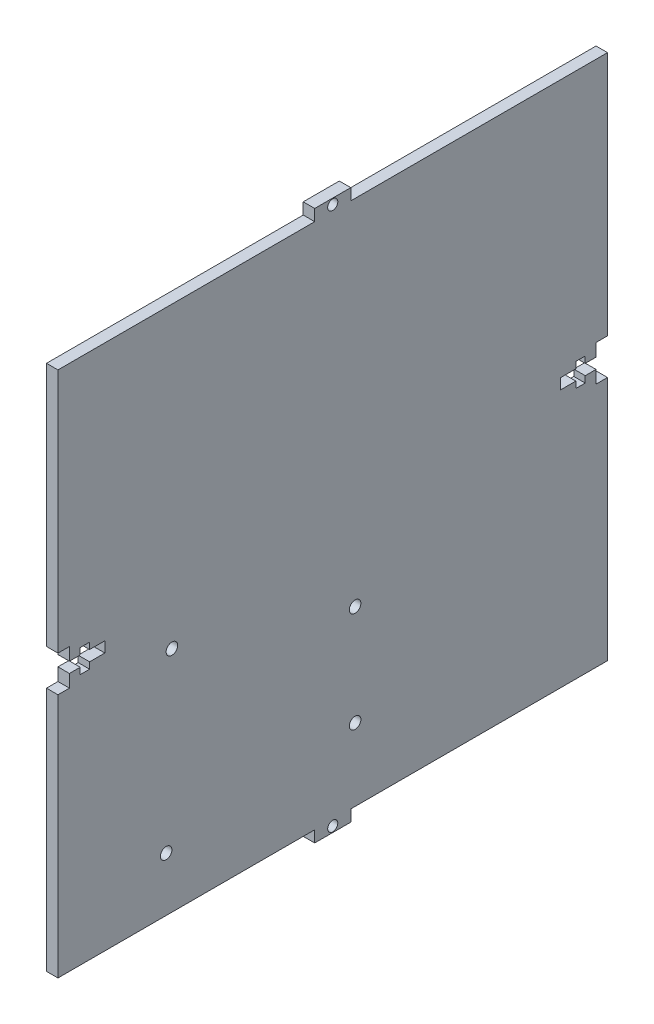
SolidWorks part; units mm, degrees
ref_plane "Front Plane" through (0, 0, 0) normal (0, 0, 1) x (1, 0, 0)
ref_plane "Top Plane" through (0, 0, 0) normal (0, 1, 0) x (1, 0, 0)
ref_plane "Right Plane" through (0, 0, 0) normal (1, 0, 0) x (0, 0, -1)
sketch "Sketch1" plane through (0, 0, 0) normal (1, 0, 0) x (0, 0, -1)
  line L1 (76.2, 73.02) -> (-76.2, 73.02)
  line L2 (76.2, 73.02) -> (76.2, -73.02)
  line L3 (76.2, -73.02) -> (-76.2, -73.02)
  line L4 (-76.2, 73.02) -> (-76.2, -73.02)
  line L5 (76.2, 73.02) -> (-76.2, -73.02) construction
  line L6 (76.2, -73.02) -> (-76.2, 73.02) construction
  point P0 (0, 0)
  dimension "D1" = 146.04
  dimension "D2" = 152.4
extrude "Boss-Extrude1" add sketch "Sketch1" along normal blind 3.18
sketch "Sketch3" plane through (0, 0, 0) normal (-1, 0, 0) x (0, 0, 1)
  line L1 (0, 0) -> (-76.2, 0) construction
  line L2 (-76.2, -73.02) -> (-76.2, 73.02) construction
  line L3 (0, -73.02) -> (0, 73.02) construction
  line L9 (0, 0) -> (76.2, 0) construction
  line L10 (76.2, -73.02) -> (-76.2, -73.02) construction
  line L12 (76.2, 73.02) -> (76.2, -73.02) construction
  line L13 (-76.2, 73.02) -> (76.2, 73.02) construction
  line L14 (5, -73.02) -> (-5, -73.02)
  line L15 (5, -76.2) -> (-5, -76.2)
  line L16 (5, -76.2) -> (5, -73.02)
  line L18 (-5, -76.2) -> (-5, -73.02)
  line L22 (0, -76.2) -> (0, -70.042) construction
  line L23 (5, -74.61) -> (-5, -74.61) construction
  line L27 (5, 73.02) -> (5, 76.2)
  line L28 (5, 76.2) -> (-5, 76.2)
  line L29 (-5, 73.02) -> (-5, 76.2)
  line L30 (5, 74.61) -> (-5, 74.61) construction
  line L31 (0, 73.02) -> (0, 76.2) construction
  line L32 (5, 73.02) -> (-5, 73.02)
  line L33 (0, 57.9987) -> (0, 73.02)
  circle A0 centre (0, -74.61) radius 1.4
  circle A1 centre (0, 74.61) radius 1.4
  point P31 (0, 65.5094)
  line M14 (76.2, 73.02) -> (-76.2, 73.02)
  line M16 (-76.2, -73.02) -> (76.2, -73.02)
  dimension "D5" = 2.8
  dimension "D6" = 2.8
  dimension "D2" = 10
  dimension "D3" = 3.18
  dimension "D4" = 10
  dimension "D1" = 3.18
extrude "Boss-Extrude5" add sketch "Sketch3" against normal blind 3.18 contours L29 L32 L27 L28 A1 M14 | L18 L15 L16 A0 M16
sketch "Sketch4" plane through (0, 0, 0) normal (1, 0, 0) x (0, 0, -1)
  line L2 (0, 0) -> (-76.2, 0) construction
  line L3 (-76.2, 73.02) -> (-76.2, -73.02) construction
  line L4 (-76.2, -5) -> (-76.2, 5)
  line L5 (-76.2, -5) -> (-73.02, -5)
  line L7 (-76.2, 5) -> (-73.02, 5)
  line L8 (-73.02, -5) -> (-73.02, -1.47)
  line L9 (-73.02, 1.47) -> (-73.02, 5)
  line L10 (-73.02, -1.47) -> (-70.02, -1.47)
  line L12 (-73.02, 1.47) -> (-70.02, 1.47)
  line L13 (-63.2, -1.47) -> (-63.2, 1.47)
  line L14 (-67.42, -1.47) -> (-63.2, -1.47)
  line L15 (-70.02, -3.25) -> (-67.42, -3.25)
  line L16 (-70.02, -3.25) -> (-70.02, -1.47)
  line L17 (-70.02, 3.25) -> (-67.42, 3.25)
  line L18 (-67.42, -3.25) -> (-67.42, -1.47)
  line L19 (-67.42, 1.47) -> (-63.2, 1.47)
  line L20 (-70.02, 1.47) -> (-70.02, 3.25)
  line L21 (-67.42, 1.47) -> (-67.42, 3.25)
  dimension "D1" = 3.18
  dimension "D2" = 10
  dimension "D3" = 2.94
  dimension "D4" = 6.5
  dimension "D5" = 2.6
  dimension "D6" = 13
  dimension "D7" = 3
extrude "Cut-Extrude2" cut sketch "Sketch4" along normal through all contours L18 L14 L13 L19 L21 L17 L20 L12 L9 L7 L4 L5 L8 L10 L16 L15
sketch "Sketch5" plane through (0, 0, 0) normal (-1, 0, 0) x (0, 0, 1)
  line L0 (0, 0) -> (-76.2, 0) construction
  line L1 (-76.2, -73.02) -> (-76.2, 73.02) construction
  line L2 (-70.02, -1.47) -> (-73.02, -1.47)
  line L3 (-76.2, -5) -> (-73.02, -5)
  line L4 (-76.2, -5) -> (-76.2, 5)
  line L5 (-76.2, 5) -> (-73.02, 5)
  line L6 (-73.02, -5) -> (-73.02, -1.47)
  line L7 (-63.2, -1.47) -> (-67.42, -1.47)
  line L8 (-63.2, -1.47) -> (-63.2, 1.47)
  line L9 (-63.2, 1.47) -> (-67.42, 1.47)
  line L13 (-67.42, 3.25) -> (-70.02, 3.25)
  line L14 (-67.42, 3.25) -> (-67.42, 1.47)
  line L15 (-67.42, -3.25) -> (-70.02, -3.25)
  line L16 (-70.02, 3.25) -> (-70.02, 1.47)
  line L17 (-70.02, -1.47) -> (-70.02, -3.25)
  line L20 (-67.42, -1.47) -> (-67.42, -3.25)
  line L22 (-70.02, 1.47) -> (-73.02, 1.47)
  line L23 (-73.02, 1.47) -> (-73.02, 5)
  point P9 (-39.8999, 0)
  dimension "D1" = 10
  dimension "D2" = 3.18
  dimension "D3" = 3
  dimension "D4" = 2.6
  dimension "D5" = 2.6
  dimension "D6" = 2.94
  dimension "D7" = 13
  dimension "D8" = 6.5
  dimension "D9" = 6.5
  dimension "D10" = 4.22
extrude "Cut-Extrude3" cut sketch "Sketch5" against normal through all
sketch "Sketch6" plane through (0, 0, 0) normal (-1, 0, 0) x (0, 0, 1)
  line L1 (-6.2, -52.92) -> (-6.2, -25.02) construction
  line L2 (46.2, -58.02) -> (46.2, -9.72) construction
  line L3 (76.2, -73.02) -> (5, -73.02) construction
  line L4 (76.2, -5) -> (76.2, -73.02) construction
  circle A0 centre (46.2, -58.02) radius 1.6
  circle A1 centre (44.6, -9.72) radius 1.6
  circle A2 centre (-6.2, -52.92) radius 1.6
  circle A3 centre (-6.2, -25.02) radius 1.6
  dimension "D1" = 3.2
  dimension "D2" = 5.1
  dimension "D3" = 50.8
  dimension "D4" = 48.3
  dimension "D5" = 15
  dimension "D6" = 30
  dimension "D9" = 27.9
extrude "Cut-Extrude6" cut sketch "Sketch6" against normal through all
equation "\"sheet\"= 3.18mm"
equation "\"tabW\"= 15mm"
equation "\"4-40Diam\" = 2.94mm"
equation "\"nutDiam\" = 6.5mm"
equation "\"nutThickness\"= 2.6mm"
